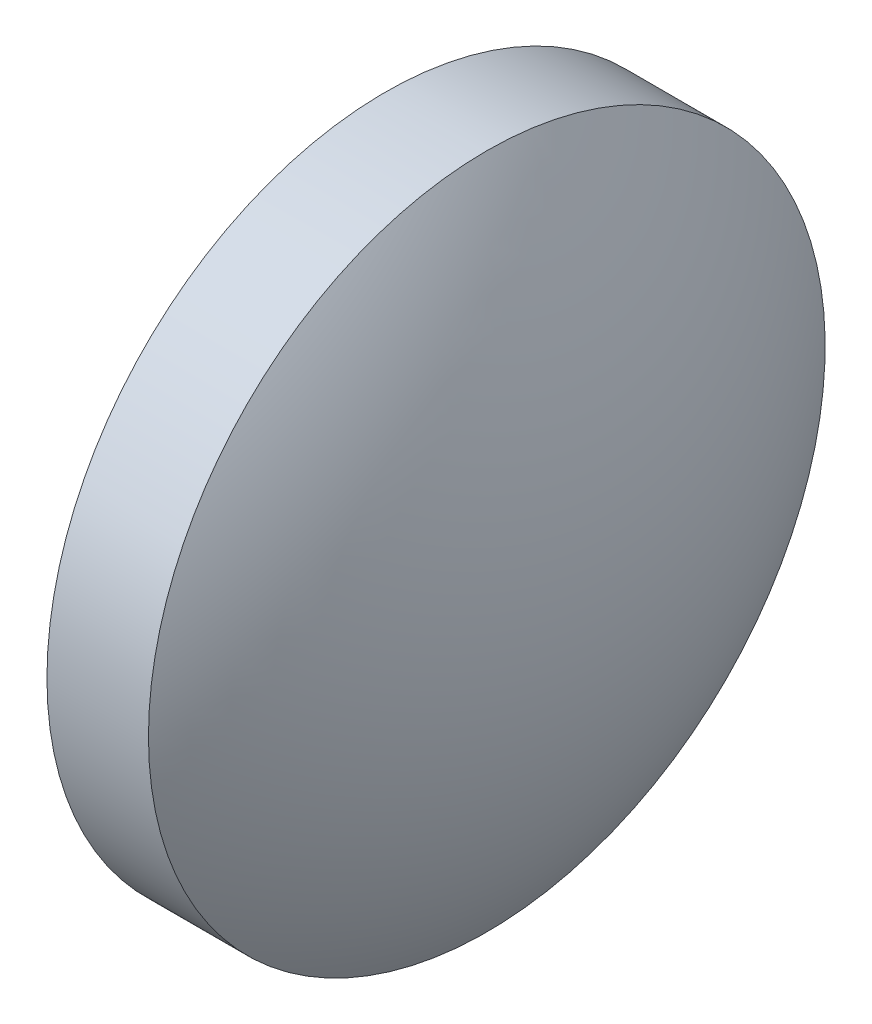
SolidWorks part; units mm, degrees
ref_plane "前视基准面" through (0, 0, 0) normal (0, 0, 1) x (1, 0, 0)
ref_plane "上视基准面" through (0, 0, 0) normal (0, 1, 0) x (1, 0, 0)
ref_plane "右视基准面" through (0, 0, 0) normal (1, 0, 0) x (0, 0, -1)
sketch "草图1" plane through (0, 0, 0) normal (0, 0, 1) x (1, 0, 0)
  line L0 (363.5196, 37.064) -> (369.1712, 37.064) construction
  line L1 (364.6618, 37.064) -> (364.6618, 42.064)
  line L2 (367.6618, 37.064) -> (364.6618, 37.064)
  line L5 (364.6618, 42.064) -> (366.1618, 42.064)
  arc A0 (367.6618, 37.064) -> (366.1618, 42.064) centre (358.5785, 37.064) ccw
revolve "旋转1" add sketch "草图1" angle 360 about L0
